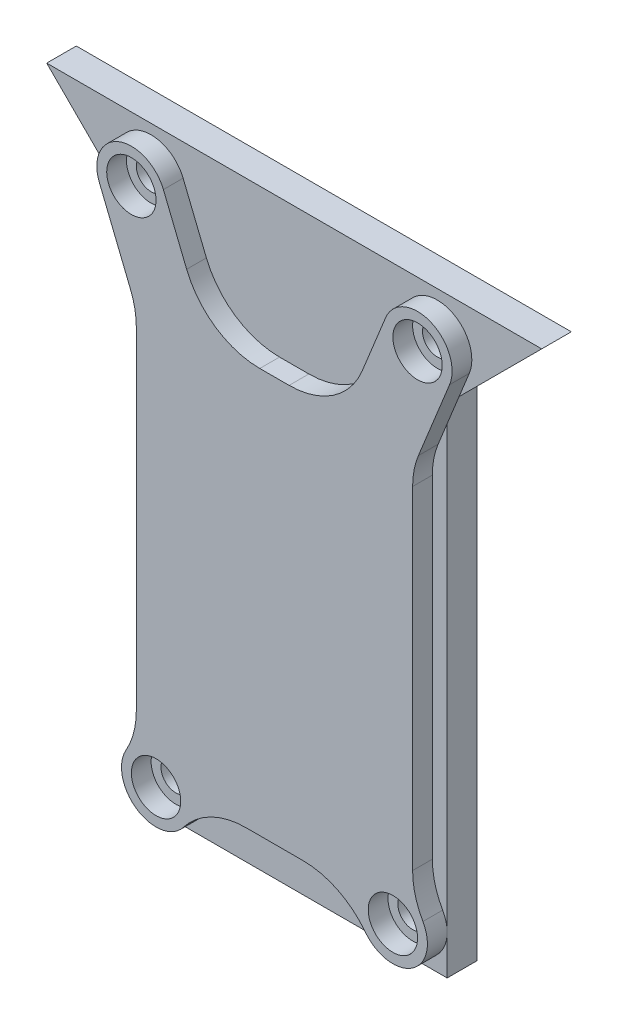
SolidWorks part; units mm, degrees
ref_plane "Front Plane" through (0, 0, 0) normal (0, 0, 1) x (1, 0, 0)
ref_plane "Top Plane" through (0, 0, 0) normal (0, 1, 0) x (1, 0, 0)
ref_plane "Right Plane" through (0, 0, 0) normal (1, 0, 0) x (0, 0, -1)
sketch "Sketch1" plane through (0, 0, 0) normal (0, 0, 1) x (1, 0, 0)
  line L1 (0, 0) -> (31, 0)
  line L2 (0, 0) -> (0, 50.4189)
  line L3 (-9.5811, 60) -> (40.5811, 60)
  line L4 (31, 0) -> (31, 50.4189)
  line L5 (40.5811, 60) -> (31, 50.4189)
  line L7 (-9.5811, 60) -> (0, 50.4189)
  circle A0 centre (30, 55.5) radius 1.5
  circle A1 centre (27.5, 44) radius 1.5
  circle A4 centre (27.5, 4) radius 1.5
  circle A5 centre (3.5, 4) radius 1.5
  circle A7 centre (3.5, 44) radius 1.5
  circle A9 centre (1, 55.5) radius 1.5
  point P1 (0, 0)
  point P2 (31, 50.4189)
  point P13 (0, 0)
  point P14 (0, 0)
  point P15 (0, 0)
  point P16 (0, 0)
  point P21 (0, 0)
  point P22 (-48.7808, 46.3753)
  point P25 (0, 0)
  point P26 (0, 0)
  point P29 (15.5, 60)
  point P30 (0, 0)
  point P31 (0, 0)
  point P32 (0, 0)
  point P34 (-1.6846, 60)
  point P35 (-1.5411, 60)
  point P36 (0, 0)
  point P37 (0, 0)
  point P38 (40.3628, 60)
  point P39 (40.5811, 60)
  point P40 (-62.9153, 53.7651)
  dimension "D4" = 3
  dimension "D5" = 21
  dimension "D6" = 2
  dimension "D7" = 2
  dimension "D8" = 21
  dimension "D9" = 2.5
  dimension "D10" = 37
  dimension "D11" = 2.8
  dimension "D12" = 29
  dimension "D13" = 14.5
  dimension "D14" = 11.5
  dimension "D15" = 3
  dimension "D1" = 45
  dimension "D2" = 45
  dimension "D3" = 31
extrude "Boss-Extrude1" add sketch "Sketch1" along normal blind 3
sketch "Sketch2" plane through (0, 0, 3) normal (0, 0, 1) x (1, 0, 0)
  line L0 (15.5, -2.1541) -> (15.5, -12.6171) construction
  line L1 (14.015, 46) -> (16.985, 46)
  line L4 (29.5, 43.3836) -> (29.5, 9.6789)
  line L5 (18.3759, 5) -> (12.6241, 5)
  line L6 (0, 0) -> (31, 0) construction
  line L7 (33.244, 54.1861) -> (30.0851, 46.3869)
  line L8 (26.756, 56.8139) -> (24.3999, 50.9968)
  line L9 (4.244, 56.8139) -> (6.6001, 50.9968)
  line L10 (-2.244, 54.1861) -> (0.9149, 46.3869)
  line L11 (1.5, 43.3836) -> (1.5, 9.6789)
  circle A0 centre (27.5, 44) radius 1.5 construction
  circle A1 centre (30, 55.5) radius 1.5 construction
  circle A3 centre (27.5, 4) radius 1.5 construction
  circle A4 centre (27.5, 4) radius 1.5 construction
  circle A5 centre (27.5, 4) radius 2.5
  circle A7 centre (30, 55.5) radius 2.5
  arc A8 (33.244, 54.1861) -> (26.756, 56.8139) centre (30, 55.5) ccw
  arc A9 (24.7231, 1.8696) -> (30.5435, 5.7284) centre (27.5, 4) ccw
  arc A10 (29.5, 43.3836) -> (30.0851, 46.3869) centre (37.5, 43.3836) cw
  arc A11 (16.985, 46) -> (24.3999, 50.9968) centre (16.985, 54) ccw
  arc A12 (24.7231, 1.8696) -> (18.3759, 5) centre (18.3759, -3) ccw
  arc A13 (30.5435, 5.7284) -> (29.5, 9.6789) centre (37.5, 9.6789) cw
  circle A14 centre (3.5, 4) radius 1.5 construction
  arc A15 (0.4565, 5.7284) -> (1.5, 9.6789) centre (-6.5, 9.6789) ccw
  arc A16 (6.2769, 1.8696) -> (12.6241, 5) centre (12.6241, -3) cw
  arc A17 (14.015, 46) -> (6.6001, 50.9968) centre (14.015, 54) cw
  arc A18 (1.5, 43.3836) -> (0.9149, 46.3869) centre (-6.5, 43.3836) ccw
  arc A19 (6.2769, 1.8696) -> (0.4565, 5.7284) centre (3.5, 4) cw
  arc A20 (-2.244, 54.1861) -> (4.244, 56.8139) centre (1, 55.5) cw
  circle A21 centre (1, 55.5) radius 2.5
  circle A22 centre (3.5, 4) radius 2.5
  point P6 (15.5, 0)
  point P7 (15.5, 46)
  point P23 (0, 0)
  point P53 (15.5, 5)
  point P54 (0, 0)
  dimension "D4" = 7
  dimension "D5" = 5
  dimension "D6" = 7
  dimension "D7" = 5
  dimension "D3" = 8
  dimension "D1" = 41
  dimension "D2" = 2
  dimension "D8" = 14
extrude "Boss-Extrude2" add sketch "Sketch2" along normal blind 2 separate body
